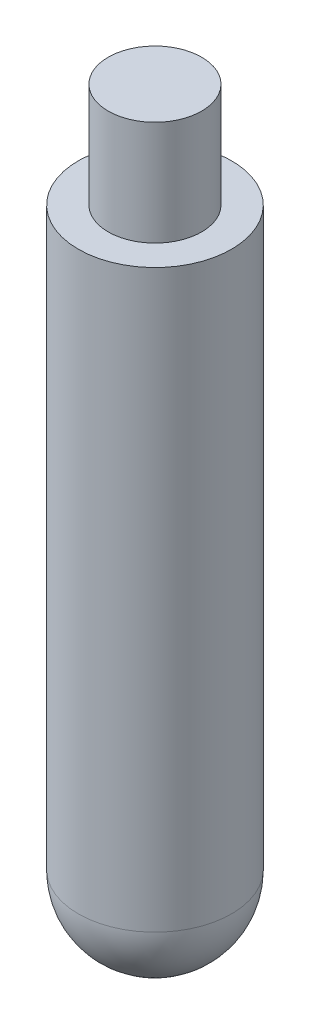
SolidWorks part; units mm, degrees
ref_plane "Alzado" through (0, 0, 0) normal (0, 0, 1) x (1, 0, 0)
ref_plane "Planta" through (0, 0, 0) normal (0, 1, 0) x (1, 0, 0)
ref_plane "Vista lateral" through (0, 0, 0) normal (1, 0, 0) x (0, 0, -1)
sketch "Croquis1" plane through (0, 0, 0) normal (0, 1, 0) x (1, 0, 0)
  circle A0 centre (0, 0) radius 2.05
  dimension "D1" = 4.1
extrude "Saliente-Extruir1" add sketch "Croquis1" along normal blind 15.4
sketch "Croquis2" plane through (0, 15.4, 0) normal (0, 1, 0) x (1, 0, 0)
  circle A0 centre (0, 0) radius 1.25
  dimension "D1" = 2.5
extrude "Saliente-Extruir2" add sketch "Croquis2" along normal blind 2.8
sketch "Croquis4" plane through (0, 0, 0) normal (0, -1, 0) x (1, 0, 0)
  line L0 (0, -2.05) -> (0, 2.05)
  circle A0 centre (0, 0) radius 2.05 construction
  arc A1 (0, 2.05) -> (0, -2.05) centre (0, 0) cw
revolve "Revolución2" add sketch "Croquis4" angle 360 about L0
